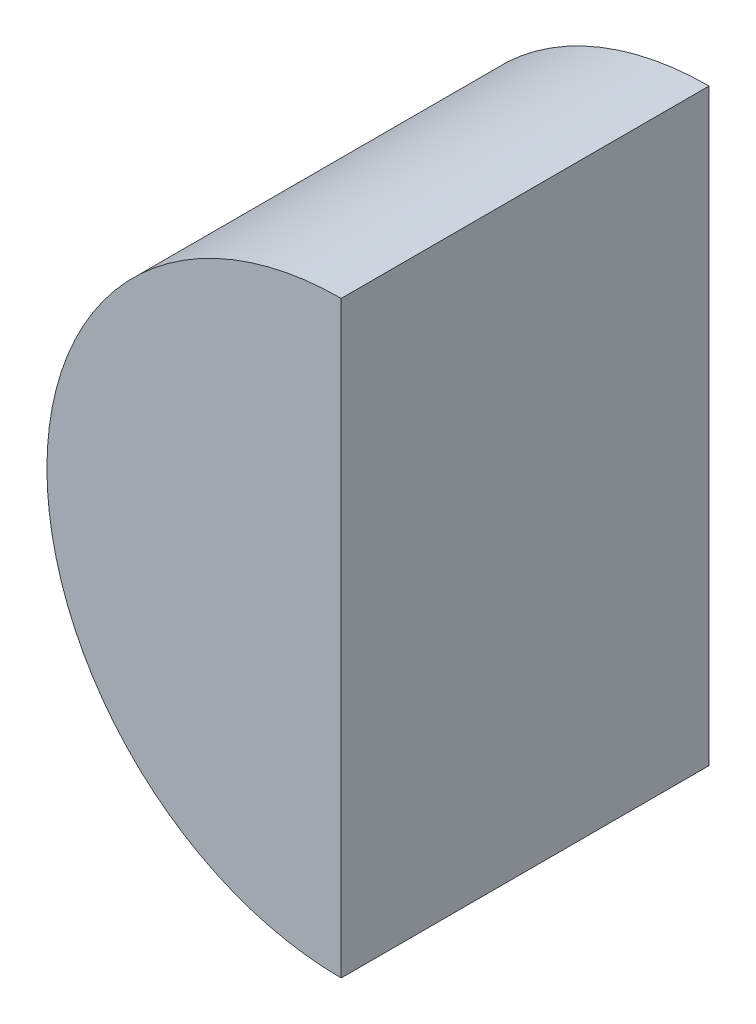
SolidWorks part; units mm, degrees
material "ABS"
ref_plane "Front Plane" through (0, 0, 0) normal (0, 0, 1) x (1, 0, 0)
ref_plane "Top Plane" through (0, 0, 0) normal (0, 1, 0) x (1, 0, 0)
ref_plane "Right Plane" through (0, 0, 0) normal (1, 0, 0) x (0, 0, -1)
sketch "Sketch1" plane through (0, 0, 0) normal (0, 0, 1) x (1, 0, 0)
  line L0 (-250, 232.5) -> (-250, 192.5) construction
  line L1 (-250, 232.5) -> (-250, 192.5)
  arc A0 (-250, 232.5) -> (-250, 192.5) centre (-250, 212.5) ccw construction
  arc A1 (-250, 232.5) -> (-250, 192.5) centre (-250, 212.5) ccw
extrude "Boss-Extrude1" add sketch "Sketch1" against normal blind 25
